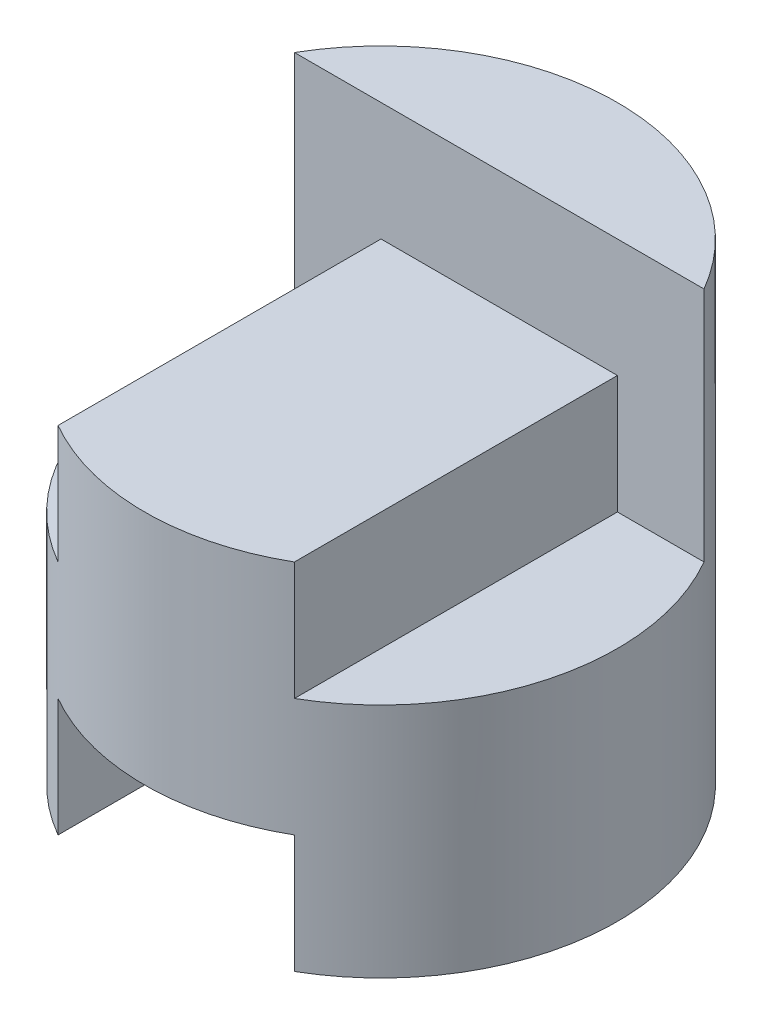
SolidWorks part; units mm, degrees
ref_plane "Front" through (0, 0, 0) normal (0, 0, 1) x (1, 0, 0)
ref_plane "Top" through (0, 0, 0) normal (0, 1, 0) x (1, 0, 0)
ref_plane "Right" through (0, 0, 0) normal (1, 0, 0) x (0, 0, -1)
sketch "Sketch1" plane through (0, 0, 0) normal (0, 1, 0) x (1, 0, 0)
  circle A0 centre (0, 0) radius 2
  dimension "D1" = 4
extrude "Boss-Extrude1" add sketch "Sketch1" along normal blind 4
sketch "Sketch2" plane through (0, 0, 0) normal (0, 0, 1) x (1, 0, 0)
  line L0 (-1, 1) -> (1, 1)
  line L4 (-1, 0) -> (-1, 1)
  line L16 (1, 0) -> (1, 1)
  line L17 (1, 0) -> (-1, 0)
  dimension "D4" = 1
extrude "Cut-Extrude1" cut sketch "Sketch2" against normal mid plane 4
sketch "Sketch3" plane through (0, 0, 0) normal (0, 0, 1) x (1, 0, 0)
  line L0 (-2, 4) -> (2, 4)
  line L1 (2, 4) -> (2, 3)
  line L2 (2, 0) -> (2, 4) construction
  line L7 (-1, 2) -> (-2, 2)
  line L8 (-2, 4) -> (-2, 0) construction
  line L9 (-2, 2) -> (-2, 4)
  line L10 (-1, 2) -> (-1, 3)
  line L12 (-1, 3) -> (0.9998, 3)
  line L13 (0.9998, 3) -> (0.9998, 2)
  line L14 (0.9998, 2) -> (2, 2)
  line L15 (2, 0) -> (2, 4) construction
  line L16 (2, 2) -> (2, 3)
  dimension "D1" = 2
  dimension "D2" = 1
extrude "Cut-Extrude2" cut sketch "Sketch3" against normal blind 1 and the other way blind 4
